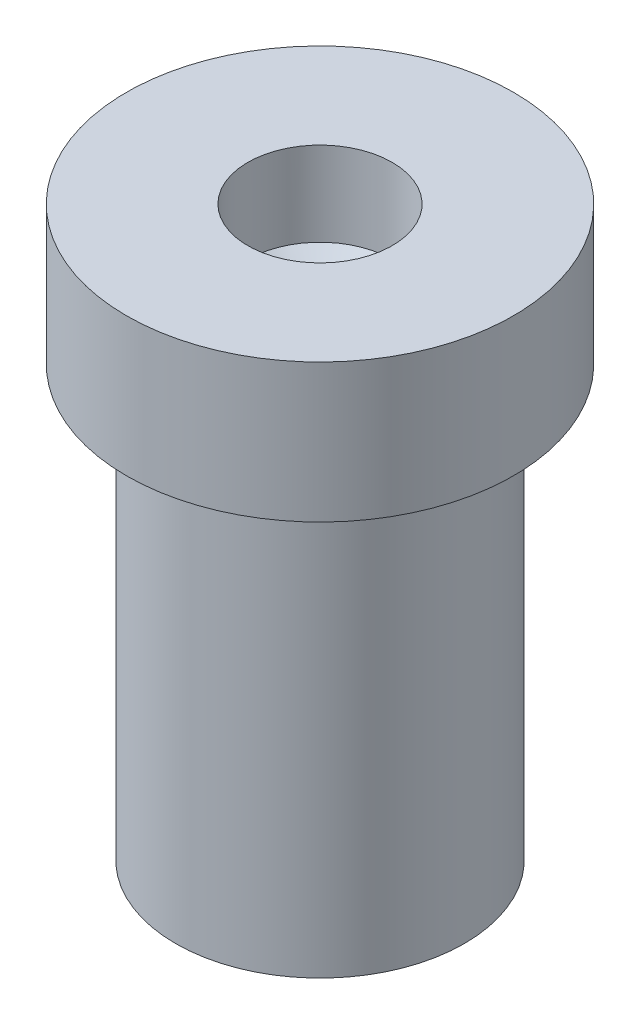
SolidWorks part; units mm, degrees
ref_plane "Front Plane" through (0, 0, 0) normal (0, 0, 1) x (1, 0, 0)
ref_plane "Top Plane" through (0, 0, 0) normal (0, 1, 0) x (1, 0, 0)
ref_plane "Right Plane" through (0, 0, 0) normal (1, 0, 0) x (0, 0, -1)
sketch "Sketch1" plane through (0, 0, 0) normal (0, 0, 1) x (1, 0, 0)
  line L0 (0, -10.425) -> (0, 12.875) construction
  line L1 (0, -10.425) -> (4.1, -10.425)
  line L2 (4.1, -10.425) -> (4.1, 1.775)
  line L3 (4.1, 1.775) -> (5.4954, 1.775)
  line L4 (5.4954, 1.775) -> (5.4954, 5.7102)
  line L5 (5.4954, 5.7102) -> (2.05, 5.7102)
  line L6 (2.05, 5.7102) -> (2.05, 3.3209)
  line L7 (0, -10.425) -> (0, 1.775)
  line L8 (2.05, 3.3209) -> (0, 1.775)
  dimension "D1" = 8.2
  dimension "D2" = 12.2
revolve "Revolve1" add sketch "Sketch1" angle 360 about L0
